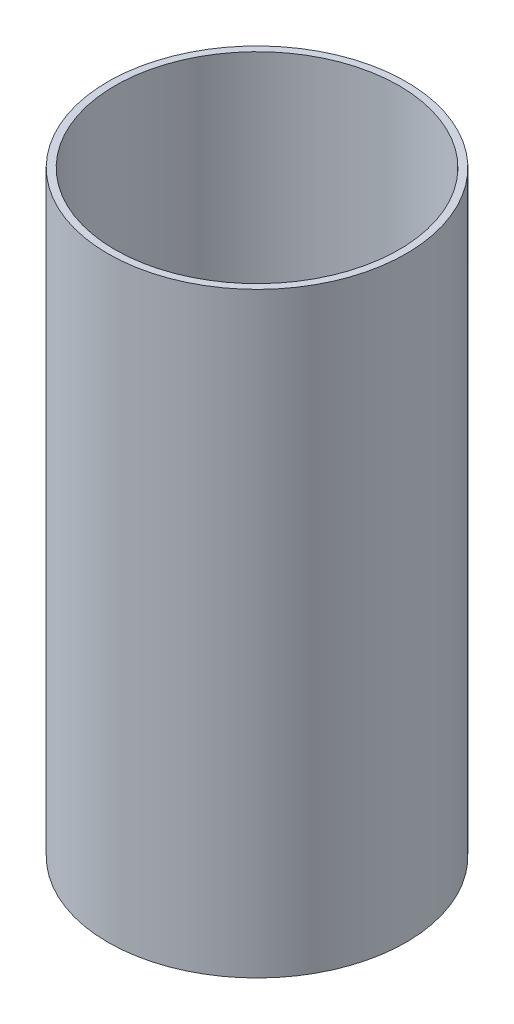
SolidWorks part; units mm, degrees
material "C-Glass Fiber"
ref_plane "Front Plane" through (0, 0, 0) normal (0, 0, 1) x (1, 0, 0)
ref_plane "Top Plane" through (0, 0, 0) normal (0, 1, 0) x (1, 0, 0)
ref_plane "Right Plane" through (0, 0, 0) normal (1, 0, 0) x (0, 0, -1)
sketch "Sketch1" plane through (0, 0, 0) normal (0, 1, 0) x (1, 0, 0)
  circle A0 centre (0, 0) radius 60.5028
  circle A1 centre (0, 0) radius 63.5
  dimension "D1" = 127
  dimension "D2" = 121.0056
extrude "Boss-Extrude1" add sketch "Sketch1" along normal blind 254
